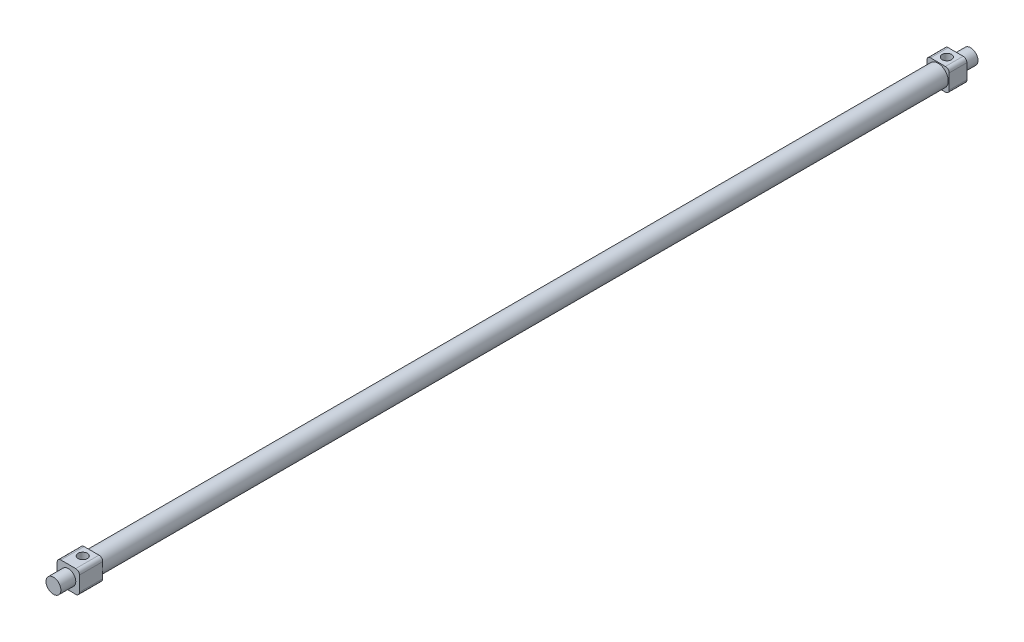
SolidWorks part; units mm, degrees
ref_plane "前视基准面" through (0, 0, 0) normal (0, 0, 1) x (1, 0, 0)
ref_plane "上视基准面" through (0, 0, 0) normal (0, 1, 0) x (1, 0, 0)
ref_plane "右视基准面" through (0, 0, 0) normal (1, 0, 0) x (0, 0, -1)
sketch "草图1" plane through (0, 0, 0) normal (0, 0, 1) x (1, 0, 0)
  line L1 (-6, -6) -> (6, -6)
  line L2 (-6, -6) -> (-6, 6)
  line L3 (-6, 6) -> (6, 6)
  line L4 (6, -6) -> (6, 6)
  line L5 (-6, -6) -> (6, 6) construction
  line L6 (-6, 6) -> (6, -6) construction
  point P0 (0, 0)
  dimension "D1" = 12
  dimension "D2" = 12
extrude "凸台-拉伸1" add sketch "草图1" along normal blind 9.5
sketch "草图2" plane through (0, 0, 9.5) normal (0, 0, 1) x (1, 0, 0)
  circle A0 centre (0, 0) radius 5.5
extrude "凸台-拉伸2" add sketch "草图2" along normal blind 455
sketch "草图3" plane through (0, 0, 464.5) normal (0, 0, 1) x (1, 0, 0)
  line L1 (-6, -6) -> (6, -6)
  line L2 (-6, -6) -> (-6, 6)
  line L3 (-6, 6) -> (6, 6)
  line L4 (6, -6) -> (6, 6)
  line L5 (-6, -6) -> (6, 6) construction
  line L6 (-6, 6) -> (6, -6) construction
  point P0 (0, 0)
extrude "凸台-拉伸3" add sketch "草图3" along normal blind 12.5
sketch "草图4" plane through (0, 0, 477) normal (0, 0, 1) x (1, 0, 0)
  circle A0 centre (0, 0) radius 4
extrude "凸台-拉伸4" add sketch "草图4" along normal blind 8
cosmetic thread "装饰螺纹线1" parameters "D2"=6.647
sketch "草图6" plane through (0, 6, 0) normal (0, 1, 0) x (1, 0, 0)
  line L0 (-6, -4.75) -> (6, -4.75) construction
  line L1 (-6, -9.5) -> (-6, 0) construction
  line L2 (6, -9.5) -> (6, 0) construction
  line L3 (-6, -469.25) -> (6, -469.25) construction
  line L5 (-6, -477) -> (-6, -464.5) construction
  line L6 (6, -477) -> (6, -464.5) construction
  line L7 (6, -464.5) -> (-6, -464.5) construction
  circle A0 centre (0, -4.75) radius 2.5
  circle A1 centre (0, -469.25) radius 2.5
  dimension "D1" = 5
  dimension "D2" = 4.75
extrude "切除-拉伸2" cut sketch "草图6" against normal up to surface (6 mm away)
cosmetic thread "装饰螺纹线2" parameters "D2"=6
cosmetic thread "装饰螺纹线3" parameters "D2"=6
fillet "圆角1" radius 2 8 edges at (6, 6, 4.75) (6, -6, 4.75) (-6, 6, 4.75) (-6, -6, 4.75) (-6, -6, 470.75) (6, -6, 470.75) (6, 6, 470.75) (-6, 6, 470.75)
sketch "草图7" plane through (0, 0, 0) normal (0, 0, -1) x (-1, 0, 0)
  circle A0 centre (0, 0) radius 4
  dimension "D1" = 8
extrude "凸台-拉伸5" add sketch "草图7" along normal blind 8
cosmetic thread "装饰螺纹线4" parameters "D1"=5, "D2"=6.647
